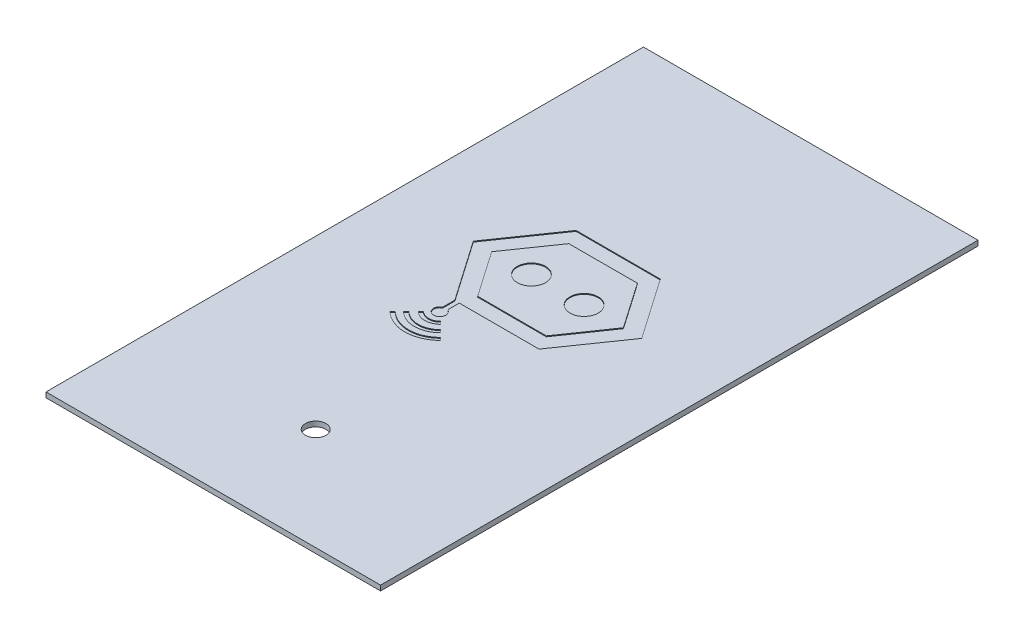
SolidWorks part; units mm, degrees
ref_plane "Front Plane" through (0, 0, 0) normal (0, 0, 1) x (1, 0, 0)
ref_plane "Top Plane" through (0, 0, 0) normal (0, 1, 0) x (1, 0, 0)
ref_plane "Right Plane" through (0, 0, 0) normal (1, 0, 0) x (0, 0, -1)
sketch "Sketch1" plane through (0, 0, 0) normal (0, 1, 0) x (1, 0, 0)
  line L1 (0, 0) -> (196, 0)
  line L2 (0, 0) -> (0, 350)
  line L3 (0, 350) -> (196, 350)
  line L4 (196, 0) -> (196, 350)
  dimension "D1" = 350
  dimension "D2" = 196
extrude "Boss-Extrude1" add sketch "Sketch1" along normal blind 3
hole_wizard "Ø12.0mm Dowel Hole1" positions "Sketch2" profile "Sketch3" hole size "Ø12.0" standard "ANSI Metric" end condition up to next
sketch "Sketch2" plane through (0, 3, 0) normal (0, 1, 0) x (1, 0, 0)
  point P0 (98, 60)
sketch "Sketch3" plane through (98, 3, -60) normal (1, 0, 0) x (0, 0, 1)
  line L0 (0, 0) -> (0, 3)
  line L1 (0, 3) -> (6, 3)
  line L2 (6, 3) -> (6, 0)
  line L5 (6, 0) -> (0, 0)
  line L11 (0, -6.35) -> (0, 107.95) construction
  dimension "Thru Hole Dia." = 12
  dimension "Thru Hole Depth" = 3
sketch "Sketch5" plane through (0, 3, 0) normal (0, 1, 0) x (1, 0, 0)
  line L0 (0, 350) -> (0, 175)
  line L1 (0, 350) -> (0, 0) construction
  line L2 (0, 175) -> (98, 175)
sketch "Sketch8" plane through (0, 3, 0) normal (0, 1, 0) x (1, 0, 0)
  line L0 (135.0175, 219.4455) -> (147.3405, 201.6788)
  line L1 (147.3405, 201.6788) -> (135.0175, 183.9123)
  line L2 (135.0175, 183.9123) -> (122.6944, 166.1457)
  line L3 (122.6944, 166.1457) -> (99.345, 166.1411)
  line L4 (99.345, 166.1411) -> (75.9955, 166.1365)
  line L5 (75.9955, 166.1365) -> (75.9955, 162.7579)
  line L6 (75.9955, 162.7579) -> (75.9955, 159.3793)
  line L7 (75.9955, 159.3793) -> (76.5384, 159.0316)
  line L8 (72.6707, 158.9927) -> (73.1648, 159.3014)
  line L9 (73.1648, 159.3014) -> (73.169, 162.8334)
  line L10 (73.169, 162.8334) -> (73.1733, 166.3654)
  line L11 (73.1733, 166.3654) -> (60.9163, 184.0221)
  line L12 (60.9163, 184.0221) -> (48.6593, 201.6788)
  line L13 (48.6593, 201.6788) -> (60.9824, 219.4454)
  line L14 (60.9824, 219.4454) -> (73.3055, 237.212)
  line L15 (73.3055, 237.212) -> (98, 237.212)
  line L16 (98, 237.212) -> (122.6944, 237.212)
  line L17 (122.6944, 237.212) -> (135.0175, 219.4455)
  line L18 (68.6619, 188.3174) -> (77.9075, 175)
  line L19 (77.9075, 175) -> (98, 175)
  line L20 (98, 175) -> (118.0925, 175)
  line L21 (118.0925, 175) -> (127.3386, 188.3174)
  line L22 (118.8404, 227.2774) -> (118.0527, 228.4021)
  line L23 (118.0527, 228.4021) -> (97.9801, 228.3799)
  line L24 (97.9801, 228.3799) -> (77.9074, 228.3576)
  line L25 (77.9074, 228.3576) -> (68.6617, 215.0403)
  line L26 (80.518, 150.6338) -> (81.2886, 149.8597)
  line L27 (81.2886, 149.8597) -> (80.7807, 149.4301)
  line L28 (69.0664, 150.6034) -> (69.8103, 151.3313)
  line L29 (69.8103, 151.3313) -> (70.2791, 150.9497)
  line L30 (84.7643, 146.3875) -> (85.534, 145.6142)
  line L31 (85.534, 145.6142) -> (84.976, 145.1079)
  line L32 (64.138, 145.3156) -> (63.9663, 145.5071)
  line L33 (63.9663, 145.5071) -> (64.729, 146.2697)
  line L34 (64.729, 146.2697) -> (65.4916, 147.0323)
  line L35 (65.4916, 147.0323) -> (66.0106, 146.5809)
  line L36 (83.2802, 146.5419) -> (83.9945, 147.1608)
  line L37 (83.9945, 147.1608) -> (84.7643, 146.3875)
  line L38 (88.6937, 142.4581) -> (89.4376, 141.7103)
  line L39 (89.4376, 141.7103) -> (89.1768, 141.4344)
  line L40 (60.1699, 141.3461) -> (59.9988, 141.537)
  line L41 (59.9988, 141.537) -> (60.7412, 142.2832)
  spline S0 degree 3 poles (76.5384, 159.0316) (77.521, 158.4025) (78.2003, 157.179) (78.2003, 156.0382) knots 0 0 0 0 1 1 1 1
  spline S1 degree 3 poles (78.2003, 156.0382) (78.2003, 153.7121) (75.8545, 151.9562) (73.6438, 152.6277) knots 0 0 0 0 1 1 1 1
  spline S2 degree 3 poles (73.6438, 152.6277) (72.1379, 153.0851) (71.0566, 154.5099) (71.0566, 156.0368) knots 0 0 0 0 1 1 1 1
  spline S3 degree 3 poles (71.0566, 156.0368) (71.0566, 157.1576) (71.7418, 158.4123) (72.6707, 158.9927) knots 0 0 0 0 1 1 1 1
  spline S4 degree 3 poles (68.6617, 215.0403) (63.5766, 207.7157) (59.416, 201.7031) (59.4161, 201.6788) knots 0 0 0 0 1 1 1 1
  spline S5 degree 3 poles (59.4161, 201.6788) (59.4161, 201.6546) (63.5767, 195.6419) (68.6619, 188.3174) knots 0 0 0 0 1 1 1 1
  spline S6 degree 3 poles (127.3386, 188.3174) (132.424, 195.6419) (136.5696, 201.6757) (136.551, 201.7257) knots 0 0 0 0 1 1 1 1
  spline S7 degree 3 poles (136.551, 201.7257) (136.5225, 201.8024) (121.2429, 223.8467) (118.8404, 227.2774) knots 0 0 0 0 1 1 1 1
  spline S8 degree 3 poles (114.4924, 210.0009) (116.428, 209.6944) (117.9222, 208.9658) (119.2403, 207.6857) knots 0 0 0 0 1 1 1 1
  spline S9 degree 3 poles (119.2403, 207.6857) (120.3763, 206.5824) (121.1423, 205.256) (121.5224, 203.7339) knots 0 0 0 0 1 1 1 1
  spline S10 degree 3 poles (121.5224, 203.7339) (121.7959, 202.6387) (121.7959, 200.8953) (121.5224, 199.8002) knots 0 0 0 0 1 1 1 1
  spline S11 degree 3 poles (121.5224, 199.8002) (121.1567, 198.3357) (120.4704, 197.1103) (119.3968, 196.0048) knots 0 0 0 0 1 1 1 1
  spline S12 degree 3 poles (119.3968, 196.0048) (118.2935, 194.8688) (116.9671, 194.1028) (115.445, 193.7227) knots 0 0 0 0 1 1 1 1
  spline S13 degree 3 poles (115.445, 193.7227) (114.8373, 193.5709) (114.4103, 193.5289) (113.4781, 193.5289) knots 0 0 0 0 1 1 1 1
  spline S14 degree 3 poles (113.4781, 193.5289) (112.546, 193.5289) (112.119, 193.5709) (111.5113, 193.7227) knots 0 0 0 0 1 1 1 1
  spline S15 degree 3 poles (111.5113, 193.7227) (109.9726, 194.1069) (108.6337, 194.8852) (107.5379, 196.0322) knots 0 0 0 0 1 1 1 1
  spline S16 degree 3 poles (107.5379, 196.0322) (106.4551, 197.1655) (105.7978, 198.3426) (105.4338, 199.8002) knots 0 0 0 0 1 1 1 1
  spline S17 degree 3 poles (105.4338, 199.8002) (105.1603, 200.8953) (105.1603, 202.6387) (105.4338, 203.7339) knots 0 0 0 0 1 1 1 1
  spline S18 degree 3 poles (105.4338, 203.7339) (105.8139, 205.256) (106.5799, 206.5824) (107.7159, 207.6857) knots 0 0 0 0 1 1 1 1
  spline S19 degree 3 poles (107.7159, 207.6857) (109.2694, 209.1943) (111.0325, 209.9398) (113.2135, 210.0101) knots 0 0 0 0 1 1 1 1
  spline S20 degree 3 poles (113.2135, 210.0101) (113.7714, 210.0281) (114.3468, 210.024) (114.4924, 210.0009) knots 0 0 0 0 1 1 1 1
  spline S21 degree 3 poles (83.6243, 210.0009) (85.56, 209.6944) (87.0541, 208.9658) (88.3722, 207.6857) knots 0 0 0 0 1 1 1 1
  spline S22 degree 3 poles (88.3722, 207.6857) (89.5083, 206.5824) (90.2743, 205.256) (90.6544, 203.7339) knots 0 0 0 0 1 1 1 1
  spline S23 degree 3 poles (90.6544, 203.7339) (90.9279, 202.6387) (90.9279, 200.8953) (90.6544, 199.8002) knots 0 0 0 0 1 1 1 1
  spline S24 degree 3 poles (90.6544, 199.8002) (90.2887, 198.3357) (89.6024, 197.1103) (88.5287, 196.0048) knots 0 0 0 0 1 1 1 1
  spline S25 degree 3 poles (88.5287, 196.0048) (87.4254, 194.8688) (86.0991, 194.1028) (84.5769, 193.7227) knots 0 0 0 0 1 1 1 1
  spline S26 degree 3 poles (84.5769, 193.7227) (83.9692, 193.5709) (83.5422, 193.5289) (82.6101, 193.5289) knots 0 0 0 0 1 1 1 1
  spline S27 degree 3 poles (82.6101, 193.5289) (81.6779, 193.5289) (81.2509, 193.5709) (80.6432, 193.7227) knots 0 0 0 0 1 1 1 1
  spline S28 degree 3 poles (80.6432, 193.7227) (79.1046, 194.1069) (77.7657, 194.8852) (76.6698, 196.0322) knots 0 0 0 0 1 1 1 1
  spline S29 degree 3 poles (76.6698, 196.0322) (75.5871, 197.1655) (74.9298, 198.3426) (74.5658, 199.8002) knots 0 0 0 0 1 1 1 1
  spline S30 degree 3 poles (74.5658, 199.8002) (74.2922, 200.8953) (74.2922, 202.6387) (74.5658, 203.7339) knots 0 0 0 0 1 1 1 1
  spline S31 degree 3 poles (74.5658, 203.7339) (74.9459, 205.256) (75.7118, 206.5824) (76.8479, 207.6857) knots 0 0 0 0 1 1 1 1
  spline S32 degree 3 poles (76.8479, 207.6857) (78.4013, 209.1943) (80.1645, 209.9398) (82.3455, 210.0101) knots 0 0 0 0 1 1 1 1
  spline S33 degree 3 poles (82.3455, 210.0101) (82.9033, 210.0281) (83.4788, 210.024) (83.6243, 210.0009) knots 0 0 0 0 1 1 1 1
  spline S34 degree 3 poles (80.7807, 149.4301) (79.7071, 148.522) (78.385, 147.8371) (76.9838, 147.4633) knots 0 0 0 0 1 1 1 1
  spline S35 degree 3 poles (76.9838, 147.4633) (76.2322, 147.2628) (75.9557, 147.2349) (74.7167, 147.2349) knots 0 0 0 0 1 1 1 1
  spline S36 degree 3 poles (74.7167, 147.2349) (73.4777, 147.2349) (73.2011, 147.2628) (72.4496, 147.4633) knots 0 0 0 0 1 1 1 1
  spline S37 degree 3 poles (72.4496, 147.4633) (71.4451, 147.7313) (70.3126, 148.2428) (69.4858, 148.8019) knots 0 0 0 0 1 1 1 1
  spline S38 degree 3 poles (69.4858, 148.8019) (68.8495, 149.2322) (68.3226, 149.6855) (68.3226, 149.8027) knots 0 0 0 0 1 1 1 1
  spline S39 degree 3 poles (68.3226, 149.8027) (68.3226, 149.8428) (68.6573, 150.2031) (69.0664, 150.6034) knots 0 0 0 0 1 1 1 1
  spline S40 degree 3 poles (70.2791, 150.9497) (72.8797, 148.8331) (76.8079, 148.8776) (79.2776, 151.0515) knots 0 0 0 0 1 1 1 1
  spline S41 degree 3 poles (79.2776, 151.0515) (79.5004, 151.2476) (79.6972, 151.408) (79.715, 151.408) knots 0 0 0 0 1 1 1 1
  spline S42 degree 3 poles (79.715, 151.408) (79.7328, 151.408) (80.0942, 151.0596) (80.518, 150.6338) knots 0 0 0 0 1 1 1 1
  spline S43 degree 3 poles (84.976, 145.1079) (82.5058, 142.8668) (79.5802, 141.5547) (76.216, 141.1793) knots 0 0 0 0 1 1 1 1
  spline S44 degree 3 poles (76.216, 141.1793) (72.2649, 140.7384) (68.1263, 141.9974) (64.9364, 144.6108) knots 0 0 0 0 1 1 1 1
  spline S45 degree 3 poles (64.9364, 144.6108) (64.5917, 144.8931) (64.2325, 145.2103) (64.138, 145.3156) knots 0 0 0 0 1 1 1 1
  spline S46 degree 3 poles (66.0106, 146.5809) (67.3137, 145.4476) (69.0064, 144.4672) (70.5274, 143.9649) knots 0 0 0 0 1 1 1 1
  spline S47 degree 3 poles (70.5274, 143.9649) (71.9657, 143.49) (72.9154, 143.3488) (74.6726, 143.3488) knots 0 0 0 0 1 1 1 1
  spline S48 degree 3 poles (74.6726, 143.3488) (76.0329, 143.3488) (76.4581, 143.3819) (77.2302, 143.5477) knots 0 0 0 0 1 1 1 1
  spline S49 degree 3 poles (77.2302, 143.5477) (79.5899, 144.0543) (81.501, 145.0001) (83.2802, 146.5419) knots 0 0 0 0 1 1 1 1
  spline S50 degree 3 poles (89.1768, 141.4344) (89.0333, 141.2826) (88.5389, 140.8414) (88.0781, 140.454) knots 0 0 0 0 1 1 1 1
  spline S51 degree 3 poles (88.0781, 140.454) (84.3623, 137.3297) (79.4527, 135.5336) (74.6285, 135.5336) knots 0 0 0 0 1 1 1 1
  spline S52 degree 3 poles (74.6285, 135.5336) (69.8054, 135.5336) (64.9066, 137.3252) (61.1788, 140.4524) knots 0 0 0 0 1 1 1 1
  spline S53 degree 3 poles (61.1788, 140.4524) (60.718, 140.8389) (60.264, 141.2411) (60.1699, 141.3461) knots 0 0 0 0 1 1 1 1
  spline S54 degree 3 poles (60.7412, 142.2832) (61.1495, 142.6937) (61.5043, 143.0281) (61.5296, 143.0264) knots 0 0 0 0 1 1 1 1
  spline S55 degree 3 poles (61.5296, 143.0264) (61.555, 143.0247) (61.9862, 142.6691) (62.4878, 142.2363) knots 0 0 0 0 1 1 1 1
  spline S56 degree 3 poles (62.4878, 142.2363) (66.8268, 138.4929) (72.6098, 136.9804) (78.2885, 138.1038) knots 0 0 0 0 1 1 1 1
  spline S57 degree 3 poles (78.2885, 138.1038) (81.5103, 138.7411) (84.3225, 140.1243) (86.8924, 142.3356) knots 0 0 0 0 1 1 1 1
  spline S58 degree 3 poles (86.8924, 142.3356) (87.4487, 142.8143) (87.9141, 143.2059) (87.9268, 143.2059) knots 0 0 0 0 1 1 1 1
  spline S59 degree 3 poles (87.9268, 143.2059) (87.9394, 143.2059) (88.2845, 142.8694) (88.6937, 142.4581) knots 0 0 0 0 1 1 1 1
extrude "Cut-Extrude1" cut sketch "Sketch8" against normal blind 0.5 contours S3 S2 S1 S0 L7 L6 L5 L4 L3 L2 L1 L0 L17 L16 L15 L14 L13 L12 L11 L10 L9 L8 S7 S6 L21 L20 L19 L18 S5 S4 L25 L24 L23 L22 | S33 S32 S31 S30 S29 S28 S27 S26 S25 S24 S23 S22 S21 | S20 S19 S18 S17 S16 S15 S14 S13 S12 S11 S10 S9 S8 | S49 S48 S47 S46 L35 L34 L33 L32 S45 S44 S43 L31 L30 L37 L36 | S40 S41 S42 L26 L27 S34 S35 S36 S37 S38 S39 L28 L29 | S52 S53 L40 L41 S54 S55 S56 S57 S58 S59 L38 L39 S50 S51
